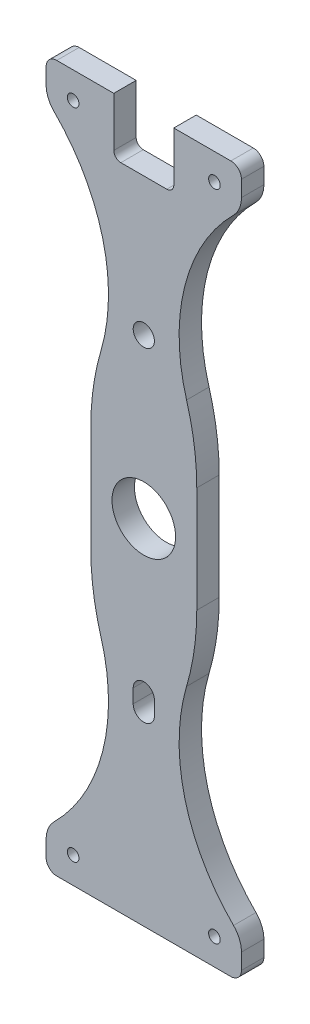
SolidWorks part; units mm, degrees
material "6061-T6 (SS)"
ref_plane "Front Plane" through (0, 0, 0) normal (0, 0, 1) x (1, 0, 0)
ref_plane "Top Plane" through (0, 0, 0) normal (0, 1, 0) x (1, 0, 0)
ref_plane "Right Plane" through (0, 0, 0) normal (1, 0, 0) x (0, 0, -1)
sketch "Sketch1" plane through (0, 0, 0) normal (0, 0, 1) x (1, 0, 0)
  line L5 (-15, 0) -> (15, 0) construction
  line L6 (0, -43.0352) -> (0, -46.957) construction
  line L10 (3, -43.0352) -> (3, -46.957)
  line L13 (240, 100) -> (240, -100) construction
  line L14 (-3, -43.0352) -> (-3, -46.957)
  line L15 (-15, 15) -> (-15, -15)
  line L18 (-24.65, -100) -> (24.65, -100)
  line L21 (15, -15) -> (15, 15)
  line L23 (27.65, 92.5) -> (27.65, 97)
  line L24 (24.65, 100) -> (-24.65, 100)
  line L25 (-27.65, 97) -> (-27.65, 92.5)
  line L27 (27.65, -92.5) -> (27.65, -97)
  line L28 (-27.65, -97) -> (-27.65, -92.5)
  line L29 (-3.92, 79.4898) -> (-3.92, -120.5102) construction
  line L30 (0, 100) -> (0, 0) construction
  line L31 (-10, -49.8891) -> (-10, -92.5) construction
  line L32 (-10, -92.5) -> (10, -92.5) construction
  line L33 (10, -92.5) -> (10, -49.8891) construction
  line L34 (25.4094, 87.0906) -> (0, 61.6813) construction
  circle A0 centre (0, 0) radius 9
  circle A13 centre (0, 44.9961) radius 4.9609 construction
  circle A14 centre (0, -44.9961) radius 4.9609 construction
  circle A18 centre (0, 44.9961) radius 3
  arc A19 (3, -43.0352) -> (-3, -43.0352) centre (0, -43.0352) ccw
  arc A20 (-3, -46.957) -> (3, -46.957) centre (0, -46.957) ccw
  circle A21 centre (20, 92.5) radius 1.65
  circle A22 centre (-20, 92.5) radius 1.65
  circle A23 centre (-20, -92.5) radius 1.65
  circle A24 centre (20, -92.5) radius 1.65
  arc A25 (-27.65, 92.5) -> (-25.4094, 87.0906) centre (-20, 92.5) ccw
  arc A27 (27.65, 92.5) -> (25.4094, 87.0906) centre (20, 92.5) cw
  arc A29 (27.65, -92.5) -> (25.4094, -87.0906) centre (20, -92.5) ccw
  arc A32 (-27.65, -92.5) -> (-25.4094, -87.0906) centre (-20, -92.5) cw
  arc A33 (15, -15) -> (12.1176, -35.1132) centre (-56.6143, -15) cw
  arc A34 (12.1176, -35.1132) -> (25.4094, -87.0906) centre (62.6109, -49.8891) ccw
  arc A35 (-12.1176, -35.1132) -> (-25.4094, -87.0906) centre (-62.6109, -49.8891) cw
  arc A36 (-15, -15) -> (-12.1176, -35.1132) centre (56.6143, -15) ccw
  arc A37 (-15, 15) -> (-12.1176, 35.1132) centre (56.6143, 15) cw
  arc A38 (-12.1176, 35.1132) -> (-25.4094, 87.0906) centre (-62.6109, 49.8891) ccw
  arc A39 (12.1176, 35.1132) -> (25.4094, 87.0906) centre (62.6109, 49.8891) cw
  arc A40 (15, 15) -> (12.1176, 35.1132) centre (-56.6143, 15) ccw
  arc A42 (-24.65, 100) -> (-27.65, 97) centre (-24.65, 97) ccw
  arc A43 (27.65, 97) -> (24.65, 100) centre (24.65, 97) ccw
  arc A44 (-27.65, -97) -> (-24.65, -100) centre (-24.65, -97) ccw
  arc A45 (27.65, -97) -> (24.65, -100) centre (24.65, -97) cw
  point P6 (0, -44.9961)
  point P64 (0, -92.5)
  point P69 (-27.65, 100)
  point P72 (27.65, 100)
  point P75 (-27.65, -100)
  point P78 (27.65, -100)
  dimension "D1" = 18
  dimension "D9" = 9.9219
  dimension "D2" = 6
  dimension "D3" = 3.3
  dimension "D11" = 3
  dimension "D8" = 89.9922
  dimension "D4" = 220
  dimension "D6" = 185
  dimension "D7" = 200
  dimension "D10" = 6
  dimension "D5" = 40
  dimension "D13" = 30
  dimension "D14" = 20
  dimension "D15" = 30
  dimension "D16" = 45
extrude "Boss-Extrude1" add sketch "Sketch1" along normal blind 6.35
sketch "Sketch2" plane through (0, 0, 0) normal (0, 0, -1) x (-1, 0, 0)
  line L0 (-16.1644, 74.6) -> (16.1644, 74.6)
  line L1 (-24.65, 100) -> (24.65, 100) construction
  line L2 (55, 0) -> (-55, 0) construction
  line L3 (-16.1644, -74.6) -> (16.1644, -74.6)
  arc A0 (25.4094, 87.0906) -> (12.1176, 35.1132) centre (62.6109, 49.8891) ccw construction
  arc A1 (-12.1176, 35.1132) -> (-25.4094, 87.0906) centre (-62.6109, 49.8891) ccw construction
  dimension "D1" = 25.4
split line "Split Line1"
sketch "Sketch3" plane through (0, 0, 6.35) normal (0, 0, 1) x (1, 0, 0)
  line L0 (24.65, 100) -> (-24.65, 100) construction
  line L1 (-7.5, 100) -> (7.5, 100) construction
  line L2 (-7.5, 100) -> (-7.5, 85) construction
  line L3 (-7.5, 85) -> (7.5, 85) construction
  line L4 (7.5, 100) -> (7.5, 85) construction
  line L5 (-8.5, 101) -> (-8.5, 86)
  line L6 (-6.5, 84) -> (6.5, 84)
  line L7 (8.5, 101) -> (8.5, 86)
  line L9 (-8.5, 101) -> (8.5, 101) construction
  line L10 (-8.5, 84) -> (8.5, 84) construction
  line L11 (8.5, 101) -> (8.5, 84) construction
  line L12 (-8.5, 101) -> (-8.5, 84) construction
  line L13 (-8.5, 101) -> (8.5, 101)
  arc A0 (6.5, 84) -> (8.5, 86) centre (6.5, 86) ccw
  arc A1 (-8.5, 86) -> (-6.5, 84) centre (-6.5, 86) ccw
  point P6 (0, 100)
  dimension "D3" = 2
  dimension "D1" = 15
  dimension "D2" = 1
extrude "Cut-Extrude1" cut sketch "Sketch3" against normal blind 10
equation "\"frame inside height\"= 200mm'`"
equation "\"hole spacing\"= 20mm"
equation "\"top hole to bottom hole\"= \"frame inside height\" - 7.5mm * 2"
equation "\"D6@Sketch1\"=\"top hole to bottom hole\""
equation "\"D7@Sketch1\"=\"frame inside height\""
equation "\"D5@Sketch1\"=\"hole spacing\"*2"
